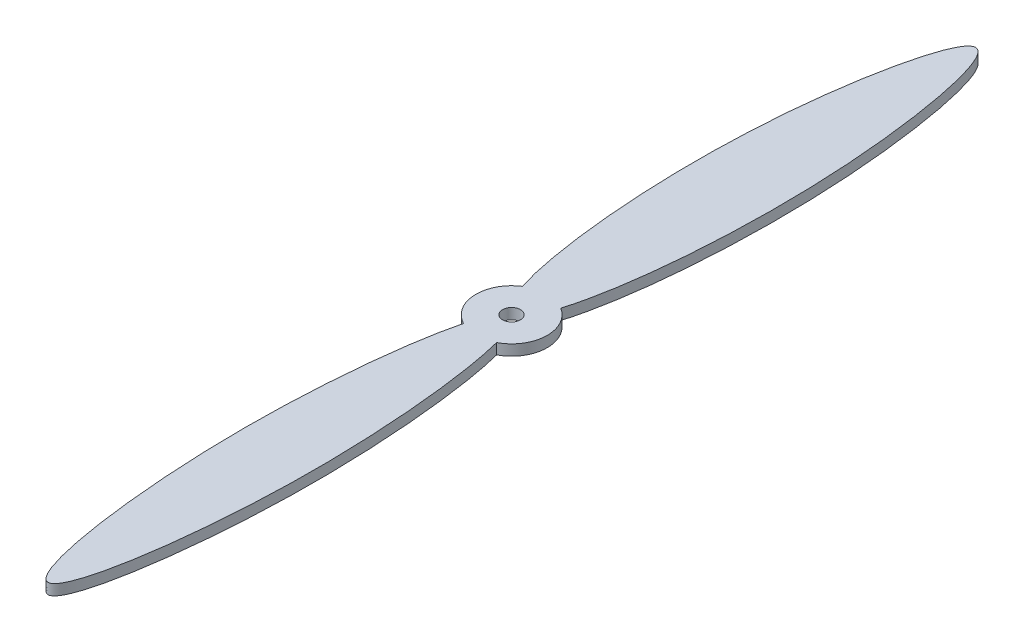
SolidWorks part; units mm, degrees
material "ABS"
ref_plane "Front Plane" through (0, 0, 0) normal (0, 0, 1) x (1, 0, 0)
ref_plane "Top Plane" through (0, 0, 0) normal (0, 1, 0) x (1, 0, 0)
ref_plane "Right Plane" through (0, 0, 0) normal (1, 0, 0) x (0, 0, -1)
sketch "Sketch1" plane through (0, 0, 0) normal (0, 1, 0) x (1, 0, 0)
  line L1 (-12.7, 165.1) -> (12.7, 165.1) construction
  line L2 (-12.7, 165.1) -> (-12.7, -165.1) construction
  line L3 (-12.7, -165.1) -> (12.7, -165.1) construction
  line L4 (12.7, 165.1) -> (12.7, -165.1) construction
  line L5 (-12.7, 165.1) -> (12.7, -165.1) construction
  line L6 (-12.7, -165.1) -> (12.7, 165.1) construction
  arc A0 (5.8954, -11.2488) -> (6.7061, 10.7851) centre (0, 0) ccw
  arc A1 (-6.8914, 10.6676) -> (-5.8839, -11.2548) centre (0, 0) ccw
  circle A2 centre (-0.0378, -0.0007) radius 3.175
  spline S0 degree 3 poles (0, 0) (-0.0126, -0.0003) (-0.0252, -0.0006) (-0.0379, -0.0007) knots 0 0 0 0 0.000483 0.000483 0.000483 0.000483
  spline S1 degree 3 poles (-5.8839, -11.2548) (-9.8664, -26.6665) (-16.9945, -95.9293) (-0.0266, -205.1403) (16.99, -96.0142) (9.8878, -26.7053) (5.8954, -11.2488) knots 0.080129 0.080129 0.080129 0.080129 0.256247 0.499499 0.741948 0.918677 0.918677 0.918677 0.918677
  spline S2 degree 3 poles (-6.8914, 10.6676) (-13.1417, 30.5748) (-19.5877, 99.8811) (0.6269, 189.4151) (18.6842, 98.5005) (12.5539, 30.0664) (6.7061, 10.7851) knots 0.090443 0.090443 0.090443 0.090443 0.354535 0.500152 0.65703 0.910712 0.910712 0.910712 0.910712
  spline S3 degree 3 poles (0, 0) (-0.0126, -0.0001) (-0.0252, -0.0003) (-0.0378, -0.0007) knots 0.999499 0.999499 0.999499 0.999499 1 1 1 1
  point P0 (0, 0)
  dimension "D3" = 6.35
  dimension "D1" = 330.2
  dimension "D2" = 25.4
extrude "Boss-Extrude1" add sketch "Sketch1" along normal blind 3.81 contours S2 A1 S1 A0 A2
